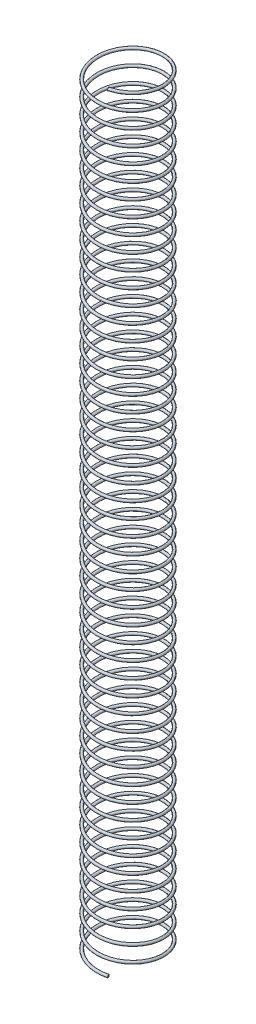
SolidWorks part; units mm, degrees
ref_plane "Front Plane" through (0, 0, 0) normal (0, 0, 1) x (1, 0, 0)
ref_plane "Top Plane" through (0, 0, 0) normal (0, 1, 0) x (1, 0, 0)
ref_plane "Right Plane" through (0, 0, 0) normal (1, 0, 0) x (0, 0, -1)
sketch "Sketch3" plane through (0, 0, 0) normal (0, 1, 0) x (1, 0, 0)
  circle A0 centre (0, 0) radius 12.192
curve "Helix/Spiral2" pitch 5.715 height 285.75 turns 50
ref_plane "Plane1" through (4.1699, 285.75, 11.4567) normal (-0.9371, 0.0744, 0.3411) x (0.34, -0.027, 0.94)
sketch "Sketch5" plane through (4.1699, 285.75, 11.4567) normal (-0.9371, 0.0744, 0.3411) x (0.34, -0.027, 0.94)
  circle A0 centre (0.002, -0.002) radius 0.508
sweep "Sweep1" add profiles "Sketch5" path "Helix/Spiral2"
